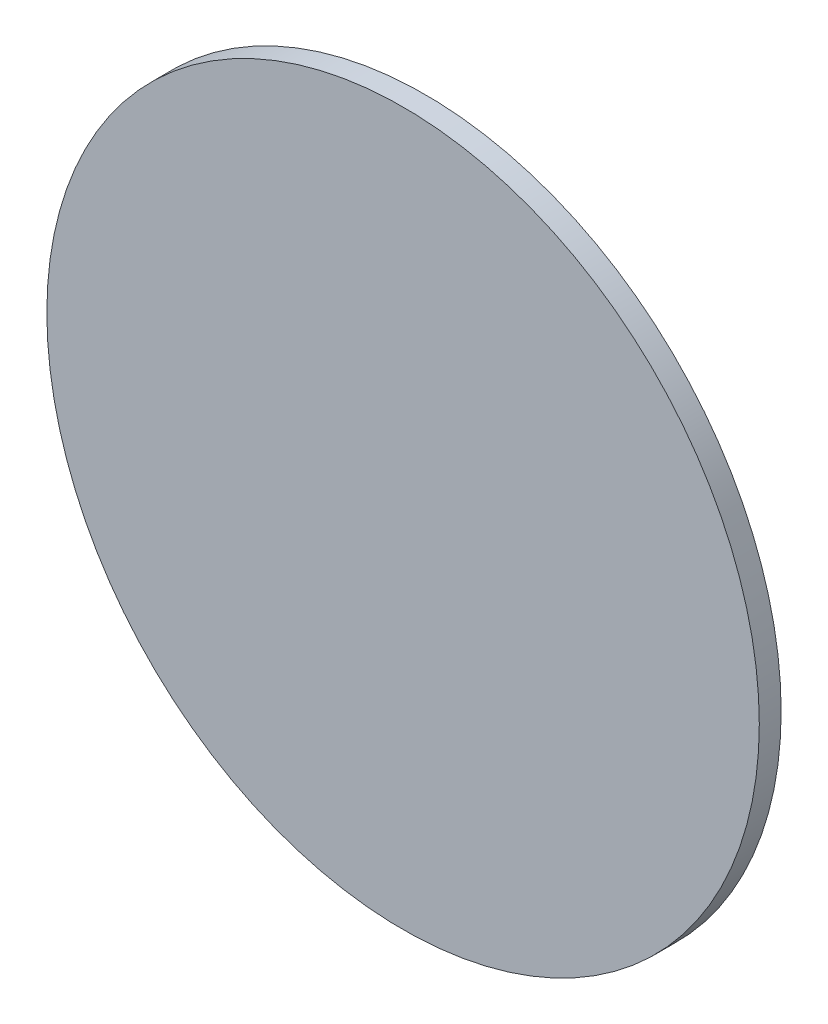
SolidWorks part; units mm, degrees
ref_plane "前视基准面" through (0, 0, 0) normal (0, 0, 1) x (1, 0, 0)
ref_plane "上视基准面" through (0, 0, 0) normal (0, 1, 0) x (1, 0, 0)
ref_plane "右视基准面" through (0, 0, 0) normal (1, 0, 0) x (0, 0, -1)
sketch "草图1" plane through (0, 0, 0) normal (0, 0, 1) x (1, 0, 0)
  circle A0 centre (-5.4578, 0) radius 37.5
  dimension "D1" = 75
extrude "凸台-拉伸1" add sketch "草图1" along normal blind 2.3
